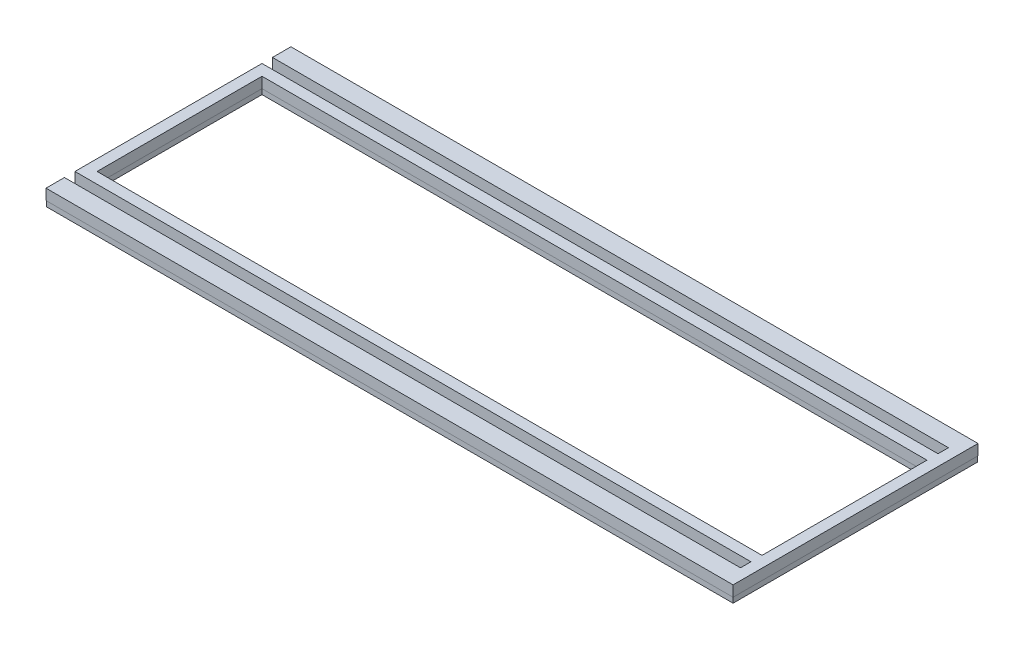
SolidWorks part; units mm, degrees
ref_plane "Front Plane" through (0, 0, 0) normal (0, 0, 1) x (1, 0, 0)
ref_plane "Top Plane" through (0, 0, 0) normal (0, 1, 0) x (1, 0, 0)
ref_plane "Right Plane" through (0, 0, 0) normal (1, 0, 0) x (0, 0, -1)
sketch "Sketch1" plane through (0, 0, 0) normal (0, 1, 0) x (1, 0, 0)
  line L0 (-203.2, 55.2482) -> (-203.2, -55.2482)
  line L1 (-203.2, 72.3646) -> (203.2, 72.3646)
  line L2 (-203.2, 72.3646) -> (-203.2, 61.649)
  line L3 (-203.2, -72.3646) -> (203.2, -72.3646)
  line L4 (203.2, 72.3646) -> (203.2, -72.3646)
  line L5 (-203.2, 72.3646) -> (203.2, -72.3646) construction
  line L6 (-203.2, -72.3646) -> (203.2, 72.3646) construction
  line L7 (-203.2, -72.3646) -> (190.5, -72.3646)
  line L8 (-203.2, -72.3646) -> (-203.2, -61.649)
  line L9 (-203.2, -61.649) -> (196.85, -61.649)
  line L11 (-203.2, 72.3646) -> (190.5, 72.3646)
  line L12 (-203.2, 72.3646) -> (-203.2, 61.649)
  line L13 (-203.2, 61.649) -> (196.85, 61.649)
  line L15 (-203.2, -61.649) -> (196.85, -61.649)
  line L17 (-203.2, -55.2482) -> (196.85, -55.2482)
  line L18 (196.85, -61.649) -> (196.85, -55.2482)
  line L19 (-203.2, 61.649) -> (196.85, 61.649)
  line L21 (-203.2, 55.2482) -> (196.85, 55.2482)
  line L22 (196.85, 61.649) -> (196.85, 55.2482)
  line L23 (-203.2, -61.649) -> (-203.2, -72.3646)
  line L25 (-196.85, -48.8982) -> (196.85, -48.8982)
  line L26 (-196.85, -48.8982) -> (-196.85, 48.8982)
  line L27 (-196.85, 48.8982) -> (196.85, 48.8982)
  line L28 (196.85, -48.8982) -> (196.85, 48.8982)
  line L29 (-196.85, -48.8982) -> (196.85, 48.8982) construction
  line L30 (-196.85, 48.8982) -> (196.85, -48.8982) construction
  point P0 (0, 0)
  point P16 (0, 0)
  dimension "D1" = 406.4
  dimension "D2" = 144.7292
  dimension "D4" = 10.7156
  dimension "D5" = 10.7156
  dimension "D6" = 6.4008
  dimension "D7" = 6.4008
  dimension "D3" = 6.35
  dimension "D8" = 6.35
  dimension "D9" = 6.35
  dimension "D10" = 6.35
extrude "Boss-Extrude1" add sketch "Sketch1" along normal mid plane 3.175
ref_plane "Plane1" [suppressed] through (0, 1.5875, 0) normal (0, 1, 0) x (1, 0, 0)
sketch "Sketch2" [suppressed] plane through (0, 1.5875, 0) normal (0, 1, 0) x (1, 0, 0)
  line L24 (-203.3016, 52.4097) -> (196.7484, 52.4097)
  line L25 (196.7484, 52.4097) -> (196.7484, 46.2121)
  line L26 (196.7484, 46.2121) -> (-203.3016, 46.2121)
  line L27 (-203.3016, 46.2121) -> (-203.3016, -46.2121)
  line L28 (-203.3016, -46.2121) -> (196.7484, -46.2121)
  line L29 (196.7484, -46.2121) -> (196.7484, -52.4097)
  line L30 (196.7484, -52.4097) -> (-203.3016, -52.4097)
  line L31 (-203.3016, -52.4097) -> (-203.3016, -63.3285)
  line L32 (-203.3016, -63.3285) -> (203.3016, -63.3285)
  line L33 (203.3016, -63.3285) -> (203.3016, 63.3286)
  line L34 (203.3016, 63.3286) -> (-203.3016, 63.3286)
  line L35 (-203.3016, 63.3286) -> (-203.3016, 52.4097)
  line L36 (-203.3016, 52.4097) -> (196.7484, 52.4097)
  line L37 (196.7484, 52.4097) -> (196.7484, 46.2121)
  line L38 (196.7484, 46.2121) -> (-203.3016, 46.2121)
  line L39 (-203.3016, 46.2121) -> (-203.3016, -46.2121)
  line L40 (-203.3016, -46.2121) -> (196.7484, -46.2121)
  line L41 (196.7484, -46.2121) -> (196.7484, -52.4097)
  line L42 (196.7484, -52.4097) -> (-203.3016, -52.4097)
  line L43 (-203.3016, -52.4097) -> (-203.3016, -63.3285)
  line L44 (-203.3016, -63.3285) -> (203.3016, -63.3285)
  line L45 (203.3016, -63.3285) -> (203.3016, 63.3286)
  line L46 (203.3016, 63.3286) -> (-203.3016, 63.3286)
  line L47 (-203.3016, 63.3286) -> (-203.3016, 52.4097)
  line L50 (196.7484, -39.6589) -> (196.7484, 39.6589)
  line L51 (-196.7484, -39.6589) -> (196.7484, -39.6589)
  line L52 (196.7484, 39.6589) -> (-196.7484, 39.6589)
  line L53 (-196.7484, 39.6589) -> (-196.7484, -39.6589)
  line L54 (196.7484, -39.6589) -> (196.7484, 39.6589)
  line L55 (-196.7484, -39.6589) -> (196.7484, -39.6589)
  line L56 (196.7484, 39.6589) -> (-196.7484, 39.6589)
  line L57 (-196.7484, 39.6589) -> (-196.7484, -39.6589)
  dimension "D1" = 0.1016
  dimension "D2" = 0.1016
extrude "Boss-Extrude2" [suppressed] add sketch "Sketch2" along normal blind 6.35
ref_plane "Plane2" [suppressed] through (0, 1.5875, 0) normal (0, 1, 0) x (1, 0, 0)
sketch "Sketch3" [suppressed] plane through (0, 1.5875, 0) normal (0, 1, 0) x (1, 0, 0)
  line L24 (-203.3016, 56.9786) -> (196.7484, 56.9786)
  line L25 (196.7484, 56.9786) -> (196.7484, 50.781)
  line L26 (196.7484, 50.781) -> (-203.3016, 50.781)
  line L27 (-203.3016, 50.781) -> (-203.3016, -50.7809)
  line L28 (-203.3016, -50.7809) -> (196.7484, -50.7809)
  line L29 (196.7484, -50.7809) -> (196.7484, -56.9785)
  line L30 (196.7484, -56.9785) -> (-203.3016, -56.9785)
  line L31 (-203.3016, -56.9785) -> (-203.3016, -67.8974)
  line L32 (-203.3016, -67.8974) -> (203.3016, -67.8974)
  line L33 (203.3016, -67.8974) -> (203.3016, 67.8974)
  line L34 (203.3016, 67.8974) -> (-203.3016, 67.8974)
  line L35 (-203.3016, 67.8974) -> (-203.3016, 56.9786)
  line L36 (-203.3016, 56.9786) -> (196.7484, 56.9786)
  line L37 (196.7484, 56.9786) -> (196.7484, 50.781)
  line L38 (196.7484, 50.781) -> (-203.3016, 50.781)
  line L39 (-203.3016, 50.781) -> (-203.3016, -50.7809)
  line L40 (-203.3016, -50.7809) -> (196.7484, -50.7809)
  line L41 (196.7484, -50.7809) -> (196.7484, -56.9785)
  line L42 (196.7484, -56.9785) -> (-203.3016, -56.9785)
  line L43 (-203.3016, -56.9785) -> (-203.3016, -67.8974)
  line L44 (-203.3016, -67.8974) -> (203.3016, -67.8974)
  line L45 (203.3016, -67.8974) -> (203.3016, 67.8974)
  line L46 (203.3016, 67.8974) -> (-203.3016, 67.8974)
  line L47 (-203.3016, 67.8974) -> (-203.3016, 56.9786)
  line L50 (196.7484, -44.2277) -> (196.7484, 44.2278)
  line L51 (-196.7484, -44.2277) -> (196.7484, -44.2277)
  line L52 (-196.7484, 44.2278) -> (-196.7484, -44.2277)
  line L53 (196.7484, 44.2278) -> (-196.7484, 44.2278)
  line L54 (196.7484, -44.2277) -> (196.7484, 44.2278)
  line L55 (-196.7484, -44.2277) -> (196.7484, -44.2277)
  line L56 (-196.7484, 44.2278) -> (-196.7484, -44.2277)
  line L57 (196.7484, 44.2278) -> (-196.7484, 44.2278)
  dimension "D1" = 0.1016
  dimension "D2" = 0.1016
extrude "Boss-Extrude3" [suppressed] add sketch "Sketch3" along normal blind 6.35
ref_plane "Plane3" through (0, 1.5875, 0) normal (0, 1, 0) x (1, 0, 0)
sketch "Sketch4" plane through (0, 1.5875, 0) normal (0, 1, 0) x (1, 0, 0)
  line L24 (-203.3016, 61.5474) -> (196.7484, 61.5474)
  line L25 (196.7484, 61.5474) -> (196.7484, 55.3498)
  line L26 (196.7484, 55.3498) -> (-203.3016, 55.3498)
  line L27 (-203.3016, 55.3498) -> (-203.3016, -55.3498)
  line L28 (-203.3016, -55.3498) -> (196.7484, -55.3498)
  line L29 (196.7484, -55.3498) -> (196.7484, -61.5474)
  line L30 (196.7484, -61.5474) -> (-203.3016, -61.5474)
  line L31 (-203.3016, -61.5474) -> (-203.3016, -72.4662)
  line L32 (-203.3016, -72.4662) -> (203.3016, -72.4662)
  line L33 (203.3016, -72.4662) -> (203.3016, 72.4662)
  line L34 (203.3016, 72.4662) -> (-203.3016, 72.4662)
  line L35 (-203.3016, 72.4662) -> (-203.3016, 61.5474)
  line L36 (-203.3016, 61.5474) -> (196.7484, 61.5474)
  line L37 (196.7484, 61.5474) -> (196.7484, 55.3498)
  line L38 (196.7484, 55.3498) -> (-203.3016, 55.3498)
  line L39 (-203.3016, 55.3498) -> (-203.3016, -55.3498)
  line L40 (-203.3016, -55.3498) -> (196.7484, -55.3498)
  line L41 (196.7484, -55.3498) -> (196.7484, -61.5474)
  line L42 (196.7484, -61.5474) -> (-203.3016, -61.5474)
  line L43 (-203.3016, -61.5474) -> (-203.3016, -72.4662)
  line L44 (-203.3016, -72.4662) -> (203.3016, -72.4662)
  line L45 (203.3016, -72.4662) -> (203.3016, 72.4662)
  line L46 (203.3016, 72.4662) -> (-203.3016, 72.4662)
  line L47 (-203.3016, 72.4662) -> (-203.3016, 61.5474)
  line L50 (196.7484, -48.7966) -> (196.7484, 48.7966)
  line L51 (-196.7484, -48.7966) -> (196.7484, -48.7966)
  line L52 (-196.7484, 48.7966) -> (-196.7484, -48.7966)
  line L53 (196.7484, 48.7966) -> (-196.7484, 48.7966)
  line L54 (196.7484, -48.7966) -> (196.7484, 48.7966)
  line L55 (-196.7484, -48.7966) -> (196.7484, -48.7966)
  line L56 (-196.7484, 48.7966) -> (-196.7484, -48.7966)
  line L57 (196.7484, 48.7966) -> (-196.7484, 48.7966)
  dimension "D1" = 0.1016
  dimension "D2" = 0.1016
extrude "Boss-Extrude4" add sketch "Sketch4" along normal blind 6.35
equation "\"D1@Sketch1\"=16.00in"
equation "\"D6@Sketch1\"=0.252"
